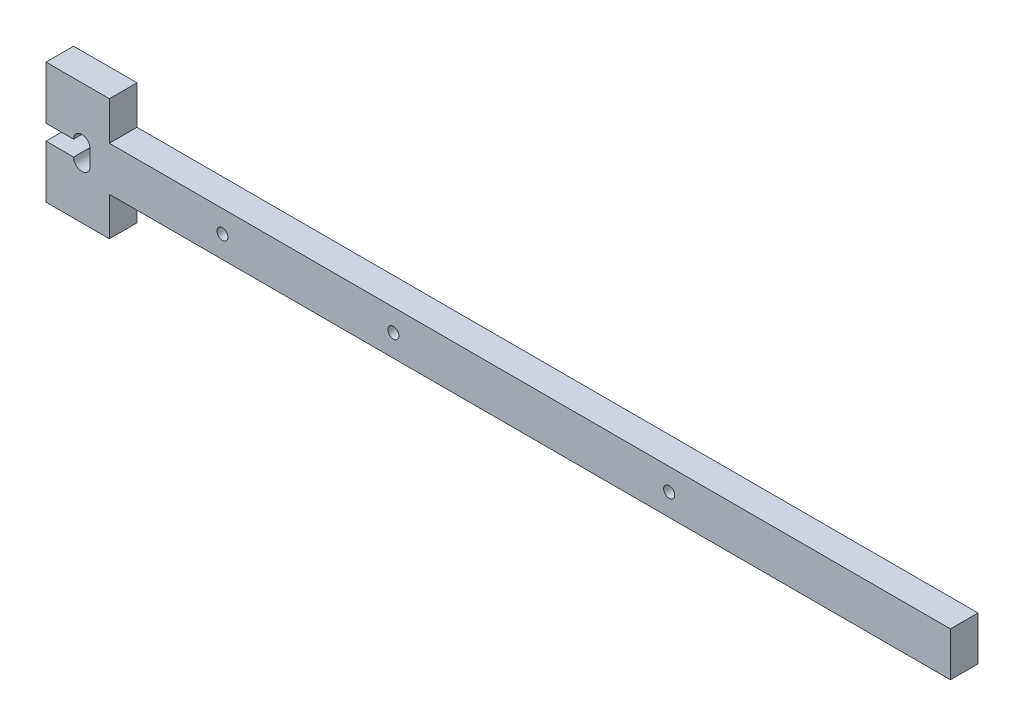
SolidWorks part; units mm, degrees
ref_plane "前视基准面" through (0, 0, 0) normal (0, 0, 1) x (1, 0, 0)
ref_plane "上视基准面" through (0, 0, 0) normal (0, 1, 0) x (1, 0, 0)
ref_plane "右视基准面" through (0, 0, 0) normal (1, 0, 0) x (0, 0, -1)
sketch "草图3" plane through (0, 0, 0) normal (0, 0, 1) x (1, 0, 0)
  line L0 (2573.6615, 4664.6534) -> (2726.1615, 4664.6346)
  line L1 (2573.6615, 4656.6344) -> (2726.1615, 4656.6344)
  line L2 (2726.1615, 4656.6344) -> (2726.1615, 4664.639)
  line L3 (2562.1615, 4649.7918) -> (2562.1615, 4671.6439)
  line L4 (2562.1615, 4662.0344) -> (2567.1615, 4662.0344)
  line L5 (2562.1615, 4659.2344) -> (2567.1615, 4659.2344)
  line L6 (2570.1615, 4659.2344) -> (2570.1615, 4662.0344)
  line L7 (2573.6615, 4664.6534) -> (2573.6615, 4671.6439)
  line L8 (2562.1615, 4660.6439) -> (2562.1615, 4649.6439)
  line L9 (2562.1615, 4649.6439) -> (2573.6615, 4649.6439)
  line L10 (2562.1615, 4671.6439) -> (2573.6615, 4671.6439)
  line L11 (2573.6615, 4649.6439) -> (2573.6615, 4656.6439)
  arc A0 (2570.1615, 4662.0344) -> (2567.1615, 4662.0344) centre (2568.6615, 4662.0344) ccw
  arc A1 (2567.1615, 4659.2344) -> (2570.1615, 4659.2344) centre (2568.6615, 4659.2344) ccw
  circle A2 centre (2625.1615, 4660.6391) radius 1
  circle A3 centre (2594.1615, 4660.6391) radius 1
  circle A4 centre (2675.1615, 4660.6391) radius 1
extrude "凸台-拉伸3" add sketch "草图3" along normal blind 5
